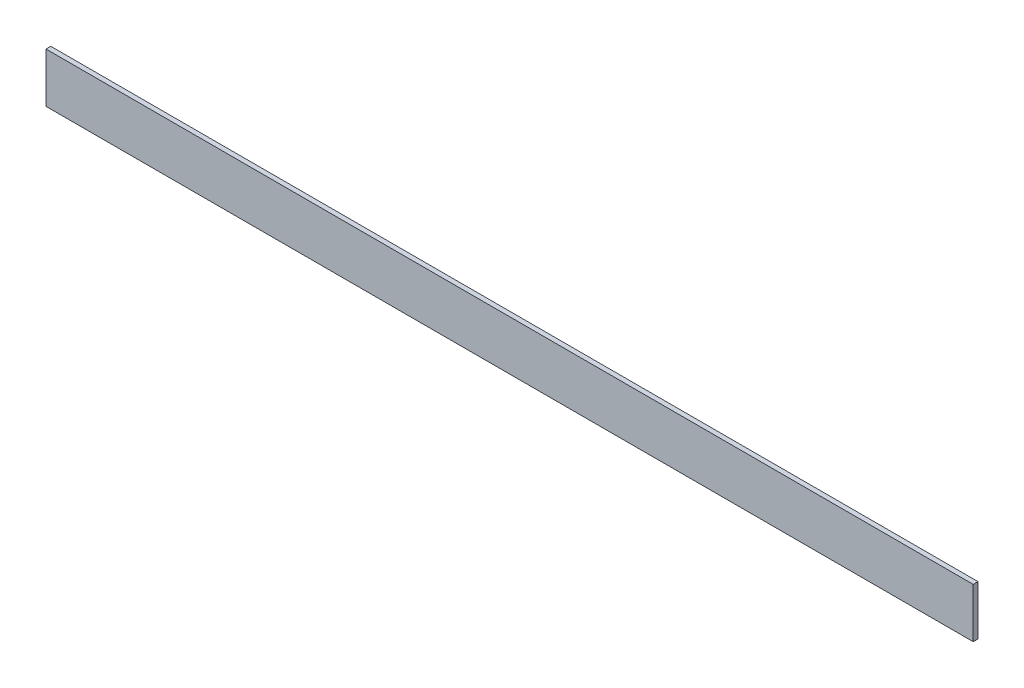
SolidWorks part; units mm, degrees
ref_plane "Front Plane" through (0, 0, 0) normal (0, 0, 1) x (1, 0, 0)
ref_plane "Top Plane" through (0, 0, 0) normal (0, 1, 0) x (1, 0, 0)
ref_plane "Right Plane" through (0, 0, 0) normal (1, 0, 0) x (0, 0, -1)
sketch "Sketch1" plane through (0, 0, 0) normal (0, 0, 1) x (1, 0, 0)
  line L1 (0, 0) -> (615.95, 0)
  line L2 (0, 0) -> (0, 33)
  line L3 (0, 33) -> (615.95, 33)
  line L4 (615.95, 0) -> (615.95, 33)
  dimension "D1" = 33
  dimension "D2" = 615.95
extrude "Boss-Extrude1" add sketch "Sketch1" along normal blind 3.175
